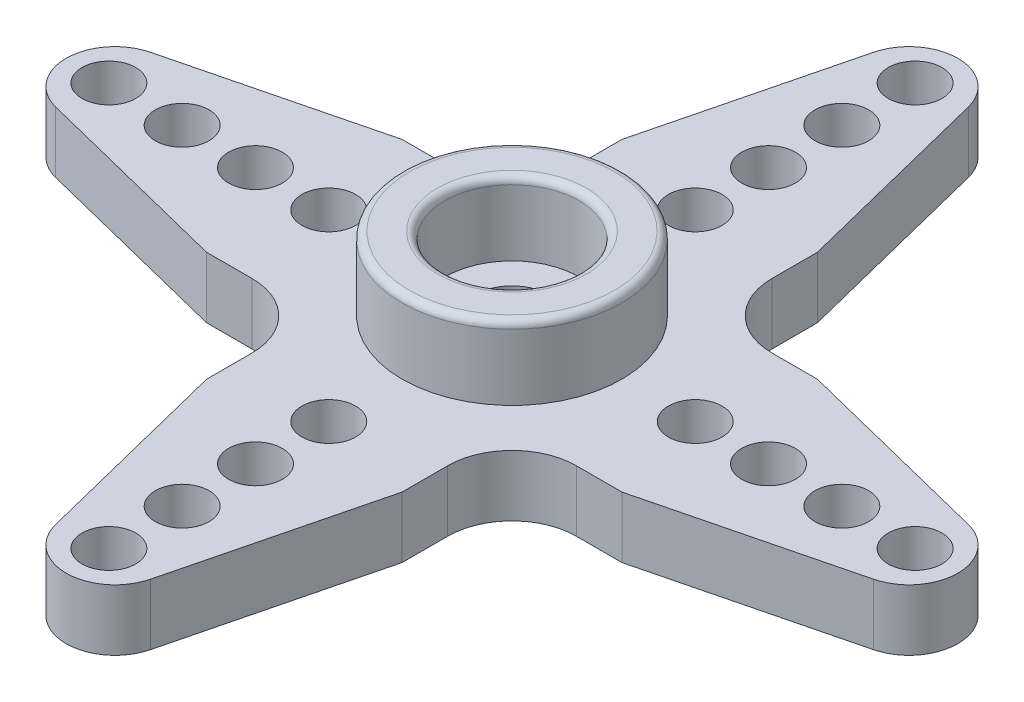
SolidWorks part; units mm, degrees
ref_plane "Alzado" through (0, 0, 0) normal (0, 0, 1) x (1, 0, 0)
ref_plane "Planta" through (0, 0, 0) normal (0, 1, 0) x (1, 0, 0)
ref_plane "Vista lateral" through (0, 0, 0) normal (1, 0, 0) x (0, 0, -1)
sketch "Croquis1" plane through (0, 0, 0) normal (0, 1, 0) x (1, 0, 0)
  line L0 (4, -8.5) -> (-4, -8.5) construction
  line L1 (0, 0) -> (0, -18.25) construction
  line L2 (-8.5, 4) -> (-6.6391, 4)
  line L3 (-6.6391, -4) -> (-8.5, -4)
  line L4 (-8.5, -4) -> (-16.7353, -1.9402)
  line L5 (-16.7353, 1.9402) -> (-8.5, 4)
  line L6 (4, 8.5) -> (4, 6.6391)
  line L7 (-4, 6.6391) -> (-4, 8.5)
  line L8 (-4, 8.5) -> (-1.9402, 16.7353)
  line L9 (4, -6.6391) -> (4, -8.5)
  line L10 (4, -8.5) -> (1.9402, -16.7353)
  line L11 (1.9402, 16.7353) -> (4, 8.5)
  line L12 (-1.9402, -16.7353) -> (-4, -8.5)
  line L13 (-4, -8.5) -> (-4, -6.6391)
  line L14 (8.5, -4) -> (6.6391, -4)
  line L15 (6.6391, 4) -> (8.5, 4)
  line L16 (8.5, 4) -> (16.7353, 1.9402)
  line L17 (16.7353, -1.9402) -> (8.5, -4)
  line L18 (-4, -6.6391) -> (-4, -5.4371) construction
  line L19 (-6.6391, -4) -> (-5.4371, -4) construction
  line L20 (-4, 6.6391) -> (-4, 5.4371) construction
  line L21 (-6.6391, 4) -> (-5.4371, 4) construction
  line L22 (4, 6.6391) -> (4, 5.4371) construction
  line L23 (6.6391, 4) -> (5.4371, 4) construction
  line L24 (6.6391, -4) -> (5.4371, -4) construction
  line L25 (4, -6.6391) -> (4, -5.4371) construction
  arc A0 (-16.7353, 1.9402) -> (-16.7353, -1.9402) centre (-16.25, 0) ccw
  arc A1 (6.6391, -4) -> (4, -6.6391) centre (6.6391, -6.6391) ccw
  arc A2 (1.9402, 16.7353) -> (-1.9402, 16.7353) centre (0, 16.25) ccw
  arc A3 (16.7353, -1.9402) -> (16.7353, 1.9402) centre (16.25, 0) ccw
  arc A4 (-1.9402, -16.7353) -> (1.9402, -16.7353) centre (0, -16.25) ccw
  arc A5 (4, 6.6391) -> (6.6391, 4) centre (6.6391, 6.6391) ccw
  arc A6 (-6.6391, 4) -> (-4, 6.6391) centre (-6.6391, 6.6391) ccw
  arc A7 (-4, -6.6391) -> (-6.6391, -4) centre (-6.6391, -6.6391) ccw
  circle A8 centre (0, 0) radius 6.75 construction
  point P35 (0, 0)
  dimension "D1" = 8
  dimension "D3" = 18.25
  dimension "D4" = 8.5
  dimension "D5" = 4
  dimension "D2" = 13.5
  dimension "D6" = 4
extrude "Saliente-Extruir1" add sketch "Croquis1" along normal blind 2.5
sketch "Croquis2" plane through (0, 2.5, 0) normal (0, 1, 0) x (1, 0, 0)
  circle A0 centre (0, 0) radius 4.5
  circle A1 centre (0, 0) radius 2.75
  dimension "D1" = 9
  dimension "D2" = 5.5
extrude "Saliente-Extruir2" add sketch "Croquis2" along normal blind 3
sketch "Croquis3" plane through (0, 0, 0) normal (0, -1, 0) x (1, 0, 0)
  circle A0 centre (0, 0) radius 1.5
  dimension "D1" = 3
extrude "Cortar-Extruir1" cut sketch "Croquis3" against normal up to next
sketch "Croquis4" plane through (0, 0, 0) normal (0, -1, 0) x (1, 0, 0)
  circle A0 centre (0, 0) radius 2.8
  dimension "D1" = 5.6
extrude "Cortar-Extruir2" cut sketch "Croquis4" against normal offset from surface (1 mm away) 1.5 up to face at (0, 2.5, 1.5)
sketch "Croquis5" plane through (0, 0, 0) normal (0, -1, 0) x (1, 0, 0)
  circle A0 centre (0, 0) radius 4.5
  circle A1 centre (0, 0) radius 3.5
  dimension "D1" = 9
  dimension "D2" = 7
extrude "Cortar-Extruir3" cut sketch "Croquis5" against normal blind 0.5
fillet "Redondeo1" radius 0.3 5 edges at (0, 0, -4.5) (0, 0, -2.8) (0, 0, -3.5) (0, 5.5, 2.75) (0, 5.5, 4.5)
sketch "Croquis6" plane through (0, 0, 0) normal (0, -1, 0) x (1, 0, 0)
  line L0 (0, 0) -> (0, -16.5) construction
  circle A0 centre (0, 0) radius 10.5 construction
  circle A1 centre (0, 0) radius 13.5 construction
  circle A2 centre (0, 0) radius 16.5 construction
  circle A3 centre (0, 0) radius 7.5 construction
  circle A4 centre (0, -16.5) radius 1.1
  circle A5 centre (0, -13.5) radius 1.1
  circle A6 centre (0, -10.5) radius 1.1
  circle A7 centre (0, -7.5) radius 1.1
  dimension "D1" = 33
  dimension "D2" = 27
  dimension "D3" = 21
  dimension "D4" = 15
  dimension "D5" = 2.2
extrude "Cortar-Extruir4" cut sketch "Croquis6" against normal up to next (2.5 mm away)
pattern_circular "MatrizC1" count 4 over 360 about axis through (0, 0, 0) along (0, 1, 0) of "Cortar-Extruir4"
